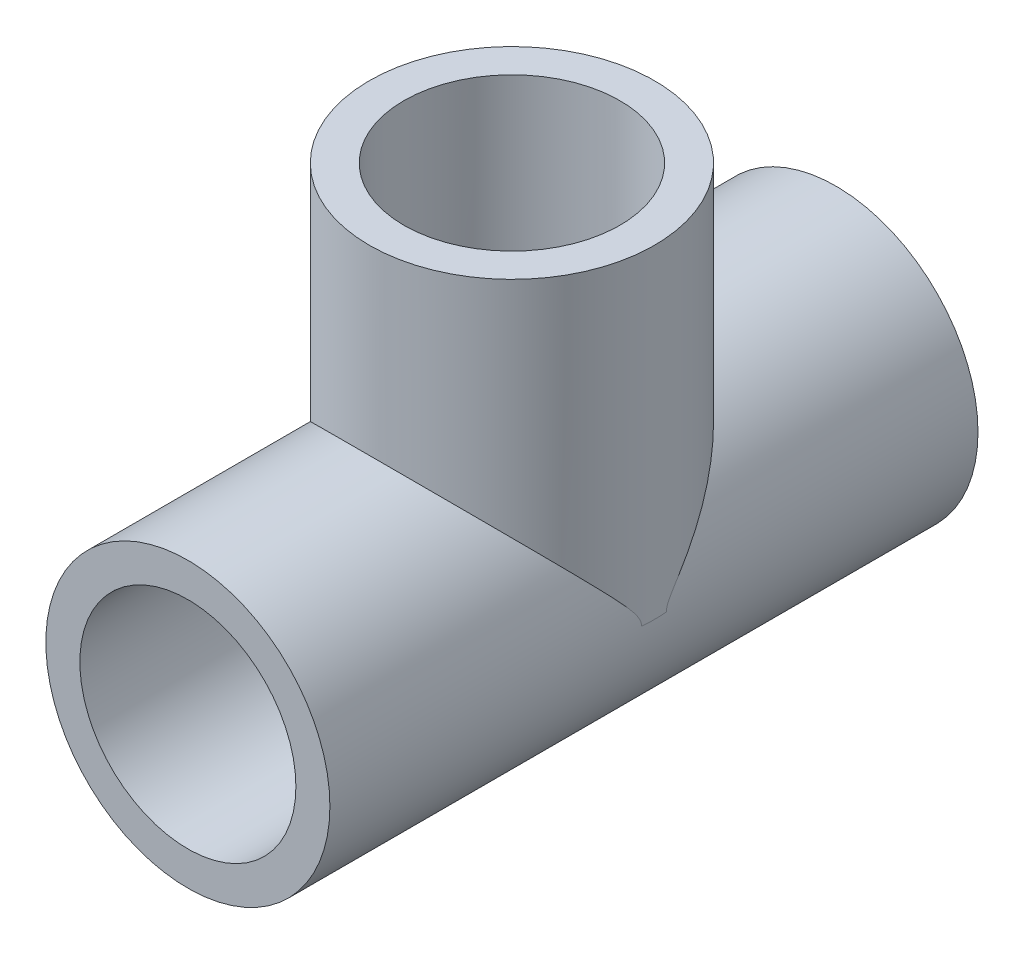
SolidWorks part; units mm, degrees
material "PVC Rigid"
ref_plane "Front Plane" through (0, 0, 0) normal (0, 0, 1) x (1, 0, 0)
ref_plane "Top Plane" through (0, 0, 0) normal (0, 1, 0) x (1, 0, 0)
ref_plane "Right Plane" through (0, 0, 0) normal (1, 0, 0) x (0, 0, -1)
sketch "Sketch1" plane through (0, 0, 0) normal (0, 0, 1) x (1, 0, 0)
  circle A0 centre (0, 0) radius 12.7
  circle A1 centre (0, 0) radius 16.7005
  dimension "D1" = 25.4
  dimension "D2" = 33.401
extrude "Boss-Extrude1" add sketch "Sketch1" along normal blind 76.2
sketch "Sketch2" plane through (0, 0, 0) normal (0, 1, 0) x (1, 0, 0)
  line L0 (-16.7005, -38.1) -> (16.7005, -38.1) construction
  line L1 (-16.7005, 0) -> (-16.7005, -76.2) construction
  line L2 (16.7005, -76.2) -> (16.7005, 0) construction
  circle A0 centre (0, -38.1) radius 16.764
  circle A1 centre (0, -38.1) radius 12.7
  dimension "D1" = 33.528
  dimension "D2" = 25.4
extrude "Boss-Extrude2" add sketch "Sketch2" along normal blind 38.1
sketch "Sketch3" plane through (0, 0, 76.2) normal (0, 0, 1) x (1, 0, 0)
  circle A0 centre (0, 0) radius 12.7
sketch "Sketch4" plane through (0, 0, 76.2) normal (0, 0, 1) x (1, 0, 0)
  line L0 (-12.7, 0) -> (12.7, 0) construction
  circle A0 centre (0, 0) radius 12.7
extrude "Cut-Extrude2" cut sketch "Sketch4" against normal through all
sketch "Sketch5" plane through (0, 38.1, 0) normal (0, 1, 0) x (1, 0, 0)
  circle A0 centre (0, -38.1) radius 12.7
extrude "Cut-Extrude3" cut sketch "Sketch5" against normal up to next
